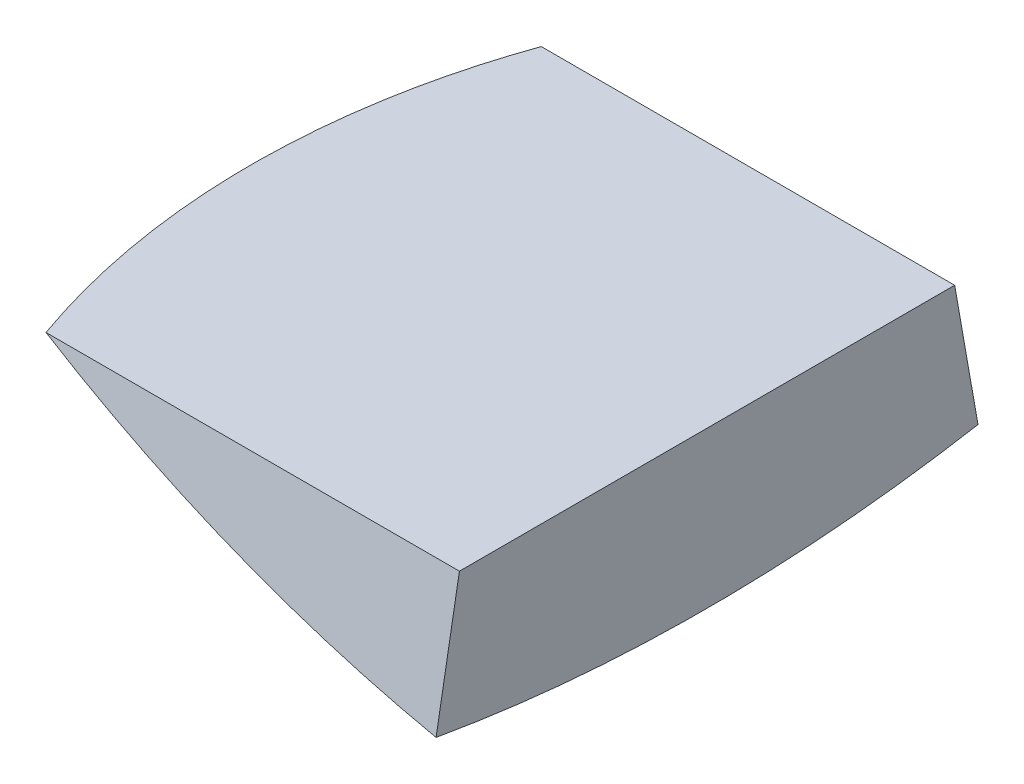
SolidWorks part; units mm, degrees
material "Polyurethane Foam Rigid"
ref_plane "Front Plane" through (0, 0, 0) normal (0, 0, 1) x (1, 0, 0)
ref_plane "Top Plane" through (0, 0, 0) normal (0, 1, 0) x (1, 0, 0)
ref_plane "Right Plane" through (0, 0, 0) normal (1, 0, 0) x (0, 0, -1)
sketch "Sketch1" plane through (0, 0, 0) normal (0, 0, 1) x (1, 0, 0)
  line L0 (-110.2666, -625.3529) -> (-110.2666, -523.7529)
  line L1 (0, 0) -> (0, -17.1989) construction
  line L2 (0, 0) -> (0, -324.9103) construction
  line L3 (0, 0) -> (-110.2666, -625.3529) construction
  line L4 (-110.2666, -523.7529) -> (-359.0374, -523.7529)
  line L5 (0, 0) -> (-376.3803, 0) construction
  line L6 (22.0533, 9.6471) -> (-365.6453, 9.6471) construction
  arc A0 (-110.2666, -625.3529) -> (-359.0374, -523.7529) centre (0, 0) cw
  dimension "D2" = 635
  dimension "D3" = 101.6
  dimension "D1" = 10
  dimension "D4" = 635
revolve "Revolve1" add sketch "Sketch1" angle 20 mid plane about L6
sketch "Sketch2" plane through (-110.2666, 0, 0) normal (1, 0, 0) x (0, 0, -1)
  line L1 (-217.2973, -484.7824) -> (194.9985, -484.7824)
  line L2 (-217.2973, -484.7824) -> (-217.2973, -561.8529)
  line L3 (-217.2973, -561.8529) -> (194.9985, -561.8529)
  line L4 (194.9985, -484.7824) -> (194.9985, -561.8529)
  arc A1 (-110.2666, -615.7058) -> (110.2666, -615.7058) centre (0, 9.6471) ccw construction
  point P4 (0, -625.3529)
  dimension "D1" = 63.5
extrude "Cut-Extrude1" cut sketch "Sketch2" against normal through all
equation "\"gapAngle\" = 10deg"
equation "\"D1@Sketch1\"=\"gapAngle\""
equation "\"LegFront\" = 25in"
equation "\"D2@Sketch1\"=\"LegFront\""
equation "\"LegSide\" = 25in"
equation "\"D4@Sketch1\"=\"LegSide\""
